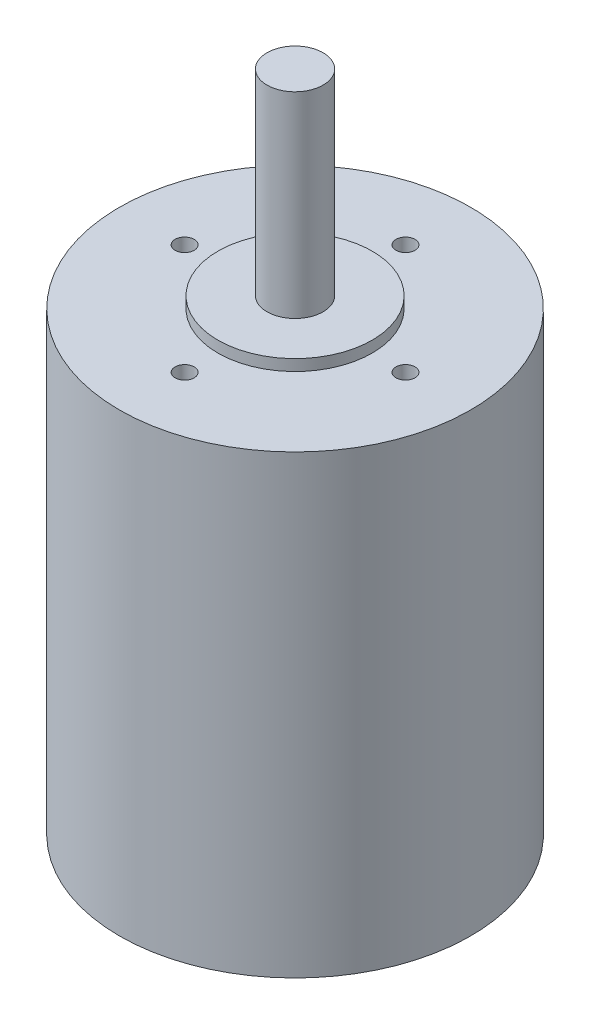
SolidWorks part; units mm, degrees
ref_plane "Front Plane" through (0, 0, 0) normal (0, 0, 1) x (1, 0, 0)
ref_plane "Top Plane" through (0, 0, 0) normal (0, 1, 0) x (1, 0, 0)
ref_plane "Right Plane" through (0, 0, 0) normal (1, 0, 0) x (0, 0, -1)
sketch "Sketch1" plane through (0, 0, 0) normal (0, 1, 0) x (1, 0, 0)
  circle A0 centre (0, 0) radius 39.751
  dimension "D1" = 79.502
extrude "Boss-Extrude1" add sketch "Sketch1" along normal blind 103.124
sketch "Sketch2" plane through (0, 103.124, 0) normal (0, 1, 0) x (1, 0, 0)
  circle A0 centre (0, 0) radius 17.4625
  dimension "D1" = 34.925
extrude "Boss-Extrude2" add sketch "Sketch2" along normal blind 2.54
sketch "Sketch3" plane through (0, 105.664, 0) normal (0, 1, 0) x (1, 0, 0)
  circle A0 centre (0, 0) radius 6.35
  dimension "D1" = 12.7
extrude "Boss-Extrude3" add sketch "Sketch3" along normal blind 44.45
sketch "Sketch4" plane through (0, 103.124, 0) normal (0, 1, 0) x (1, 0, 0)
  circle A0 centre (0, 0) radius 25 construction
  circle A1 centre (0, 25) radius 2.159
  circle A2 centre (25, 0) radius 2.159
  circle A3 centre (0, -25) radius 2.159
  circle A4 centre (-25, 0) radius 2.159
  dimension "D1" = 50
  dimension "D2" = 4.318
extrude "Cut-Extrude1" cut sketch "Sketch4" against normal blind 44.45
